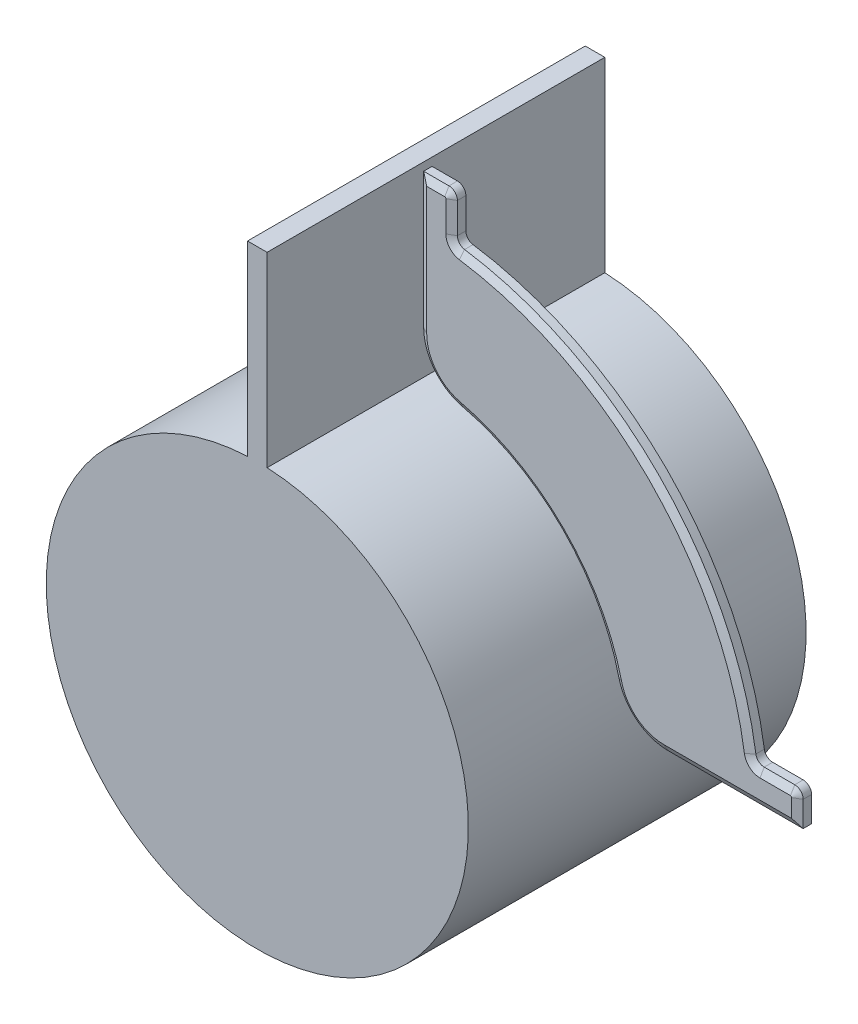
SolidWorks part; units mm, degrees
ref_plane "Front Plane" through (0, 0, 0) normal (0, 0, 1) x (1, 0, 0)
ref_plane "Top Plane" through (0, 0, 0) normal (0, 1, 0) x (1, 0, 0)
ref_plane "Right Plane" through (0, 0, 0) normal (1, 0, 0) x (0, 0, -1)
sketch "Sketch1" plane through (0, 0, 0) normal (0, 0, 1) x (1, 0, 0)
  line L0 (0, 0) -> (0, 152.4) construction
  line L1 (16.51, 131.8891) -> (16.51, 143.3585)
  line L2 (0, 0) -> (152.4, 0) construction
  line L3 (3.81, 146.5335) -> (3.81, 95.7335)
  line L4 (3.81, 146.5335) -> (13.335, 146.5335)
  line L6 (3.81, 146.5335) -> (16.51, 146.5335) construction
  line L7 (16.51, 143.3585) -> (16.51, 146.5335) construction
  line L8 (131.8891, 16.51) -> (143.3585, 16.51)
  line L9 (146.5335, 13.335) -> (146.5335, 3.81)
  line L10 (146.5335, 3.81) -> (95.7335, 3.81)
  line L11 (3.81, 146.5335) -> (0, 146.5335) construction
  line L12 (146.5335, 3.81) -> (146.5335, 0) construction
  line L13 (146.5335, 3.81) -> (146.5335, 16.51) construction
  line L14 (146.5335, 16.51) -> (143.3585, 16.51) construction
  circle A0 centre (0, 0) radius 79.375 construction
  arc A1 (19.2163, 128.7488) -> (128.7488, 19.2163) centre (0, 0) cw
  arc A2 (19.2163, 128.7488) -> (16.51, 131.8891) centre (19.685, 131.8891) cw
  arc A4 (128.7488, 19.2163) -> (131.8891, 16.51) centre (131.8891, 19.685) ccw
  arc A5 (95.7335, 3.81) -> (77.2044, 18.4355) centre (95.7335, 22.86) cw
  arc A6 (143.3585, 16.51) -> (146.5335, 13.335) centre (143.3585, 13.335) cw
  arc A7 (13.335, 146.5335) -> (16.51, 143.3585) centre (13.335, 143.3585) cw
  arc A8 (18.4355, 77.2044) -> (77.2044, 18.4355) centre (0, 0) cw
  arc A9 (3.81, 95.7335) -> (18.4355, 77.2044) centre (22.86, 95.7335) ccw
  dimension "D1" = 158.75
  dimension "D5" = 19.05
  dimension "D6" = 3.175
  dimension "D7" = 3.175
  dimension "D9" = 3.175
  dimension "D10" = 12.7
  dimension "D11" = 50.8
  dimension "D2" = 152.4
  dimension "D3" = 152.4
  dimension "D4" = 3.81
  dimension "D8" = 50.8
extrude "Boss-Extrude1" add sketch "Sketch1" along normal blind 6.35 contours A9 A8 A5 L10 L9 A6 L8 A4 A1 A2 L1 A7 L4 L3
sketch "Sketch2" plane through (0, 0, 0) normal (0, 0, 1) x (1, 0, 0)
  line L0 (0, 0) -> (0, 149.4418) construction
  line L1 (3.683, 149.4418) -> (-3.683, 149.4418)
  line L2 (-3.683, 149.4418) -> (-3.683, 79.2895)
  line L3 (3.683, 149.4418) -> (3.683, 79.2895)
  arc A1 (-3.683, 79.2895) -> (3.683, 79.2895) centre (0, 0) ccw
  point P7 (0, 149.4418)
  dimension "D2" = 79.375
  dimension "D1" = 7.366
extrude "Boss-Extrude2" add sketch "Sketch2" along normal mid plane 127 separate body
chamfer "Chamfer2" distance 2.7496 angle 30 14 edges at (7.9069, 83.9306, 0) (56.1266, 56.1266, 0) (83.9306, 7.9069, 0) (121.1335, 3.81, 0) (146.5335, 8.5725, 0) (145.6036, 15.5801, 0) (137.6238, 16.51, 0) (129.8163, 17.2799, 0) (92.0476, 92.0476, 0) (17.2799, 129.8163, 0) (16.51, 137.6238, 0) (15.5801, 145.6036, 0) (8.5725, 146.5335, 0) (3.81, 121.1335, 0)
chamfer "Chamfer3" distance 2.7496 angle 30 14 edges at (8.5725, 146.5335, 6.35) (15.5801, 145.6036, 6.35) (16.51, 137.6238, 6.35) (17.2799, 129.8163, 6.35) (92.0476, 92.0476, 6.35) (129.8163, 17.2799, 6.35) (137.6238, 16.51, 6.35) (145.6036, 15.5801, 6.35) (146.5335, 8.5725, 6.35) (121.1335, 3.81, 6.35) (83.9306, 7.9069, 6.35) (56.1266, 56.1266, 6.35) (7.9069, 83.9306, 6.35) (3.81, 121.1335, 6.35)
